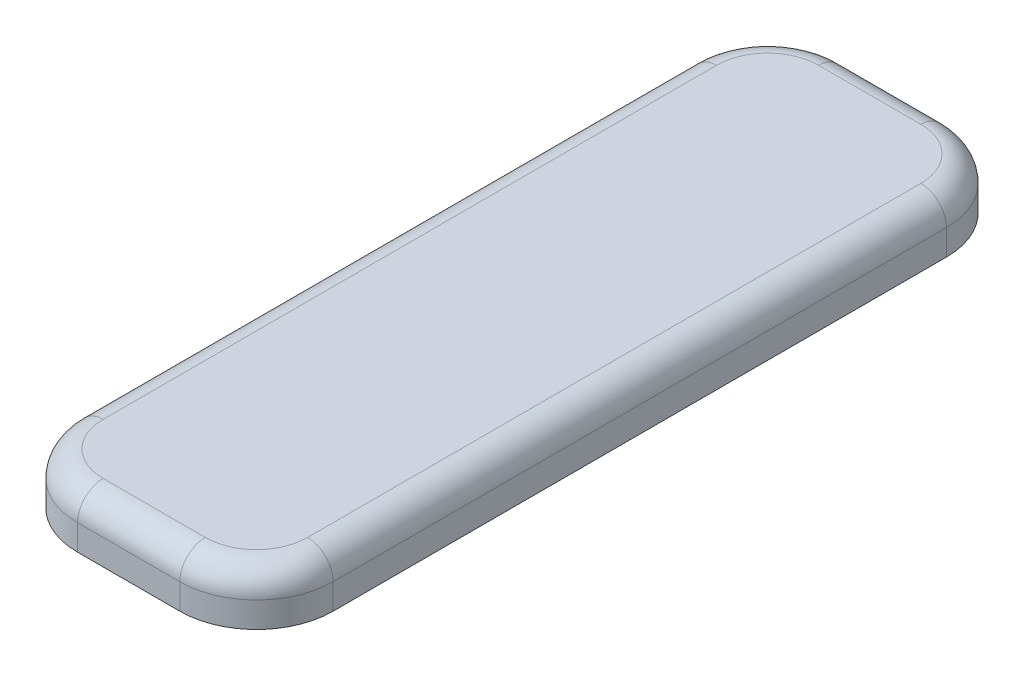
SolidWorks part; units mm, degrees
material "Polyurethane Foam Flexible"
ref_plane "Front Plane" through (0, 0, 0) normal (0, 0, 1) x (1, 0, 0)
ref_plane "Top Plane" through (0, 0, 0) normal (0, 1, 0) x (1, 0, 0)
ref_plane "Right Plane" through (0, 0, 0) normal (1, 0, 0) x (0, 0, -1)
sketch "Sketch1" plane through (0, 0, 0) normal (0, 1, 0) x (1, 0, 0)
  line L1 (-20, -150) -> (20, -150)
  line L2 (-50, -120) -> (-50, 120)
  line L3 (-20, 150) -> (20, 150)
  line L4 (50, -120) -> (50, 120)
  line L5 (-50, -150) -> (50, 150) construction
  line L6 (-50, 150) -> (50, -150) construction
  arc A0 (-50, 120) -> (-20, 150) centre (-20, 120) cw
  arc A1 (20, 150) -> (50, 120) centre (20, 120) cw
  arc A2 (50, -120) -> (20, -150) centre (20, -120) cw
  arc A3 (-20, -150) -> (-50, -120) centre (-20, -120) cw
  point P0 (0, 0)
  dimension "D3" = 30
  dimension "D1" = 100
  dimension "D2" = 300
extrude "Boss-Extrude1" add sketch "Sketch1" along normal blind 20
fillet "Fillet1" radius 10 8 edges at (0, 20, -150) (41.2132, 20, -141.2132) (50, 20, 0) (41.2132, 20, 141.2132) (0, 20, 150) (-41.2132, 20, 141.2132) (-50, 20, 0) (-41.2132, 20, -141.2132)
